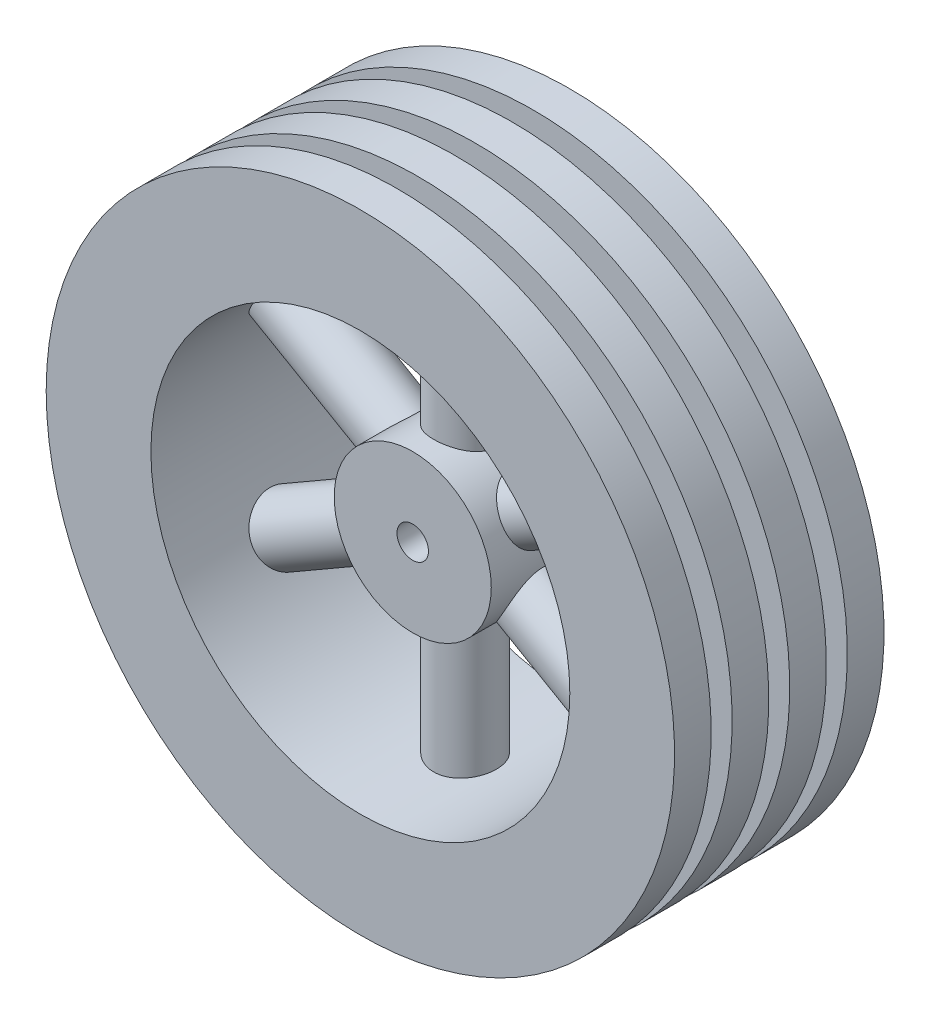
SolidWorks part; units mm, degrees
ref_plane "前基準面" through (0, 0, 0) normal (0, 0, 1) x (1, 0, 0)
ref_plane "上基準面" through (0, 0, 0) normal (0, 1, 0) x (1, 0, 0)
ref_plane "右基準面" through (0, 0, 0) normal (1, 0, 0) x (0, 0, -1)
sketch "草圖1" plane through (0, 0, 0) normal (0, 0, 1) x (1, 0, 0)
  circle A0 centre (0, 0) radius 1.5
  circle A1 centre (0, 0) radius 7.5
  dimension "D1" = 3
  dimension "D2" = 15
extrude "填料-伸長1" add sketch "草圖1" along normal blind 20
sketch "草圖2" plane through (0, 0, 0) normal (0, 1, 0) x (1, 0, 0)
  line L0 (-30, 0) -> (-20, 0)
  line L1 (-20, 0) -> (-20, -20)
  line L2 (-20, -20) -> (-30, -20)
  line L3 (-30, -20) -> (-30, -16.5)
  line L4 (-30, -16.5) -> (-22.5, -16.5)
  line L5 (-22.5, -16.5) -> (-22.5, -14.5)
  line L6 (-22.5, -14.5) -> (-30, -14.5)
  line L7 (-30, -14.5) -> (-30, -11)
  line L8 (-30, -11) -> (-22.5, -11)
  line L9 (-22.5, -11) -> (-22.5, -9)
  line L10 (-22.5, -9) -> (-30, -9)
  line L11 (-30, -9) -> (-30, -5.5)
  line L12 (-30, -5.5) -> (-22.5, -5.5)
  line L13 (-22.5, -5.5) -> (-22.5, -3.5)
  line L14 (-22.5, -3.5) -> (-30, -3.5)
  line L15 (-30, -3.5) -> (-30, 0)
  line L16 (0, 16.0606) -> (0, -28.2769) construction
  dimension "D1" = 2
  dimension "D2" = 2
  dimension "D3" = 2
  dimension "D4" = 20
  dimension "D5" = 3.5
  dimension "D6" = 3.5
  dimension "D7" = 3.5
  dimension "D8" = 30
  dimension "D9" = 30
  dimension "D10" = 30
  dimension "D11" = 22.5
  dimension "D12" = 22.5
  dimension "D13" = 22.5
  dimension "D14" = 30
  dimension "D15" = 20
ref_plane "平面1" through (0, 12, 0) normal (0, 1, 0) x (1, 0, 0)
revolve "旋轉2" add sketch "草圖2" angle 360 about L16
sketch "草圖5" plane through (0, 12, 0) normal (0, 1, 0) x (1, 0, 0)
  line L0 (0, 10.4043) -> (0, -26.7021) construction
  line L1 (7.5, 0) -> (-7.5, 0) construction
  circle A0 centre (0, -10) radius 3
  dimension "D1" = 6
  dimension "D2" = 10
extrude "填料-伸長3" add sketch "草圖5" along normal up to next and the other way up to next
pattern_circular "環狀複製排列1" count 6 over 360 about axis through (0, 0, 20) along (0, 0, -1) of "填料-伸長3"
sketch "草圖6" plane through (0, 0, 20) normal (0, 0, 1) x (1, 0, 0)
  circle A0 centre (0, 0) radius 7.5
  dimension "D1" = 15
extrude "除料-伸長1" cut sketch "草圖6" against normal blind 5
